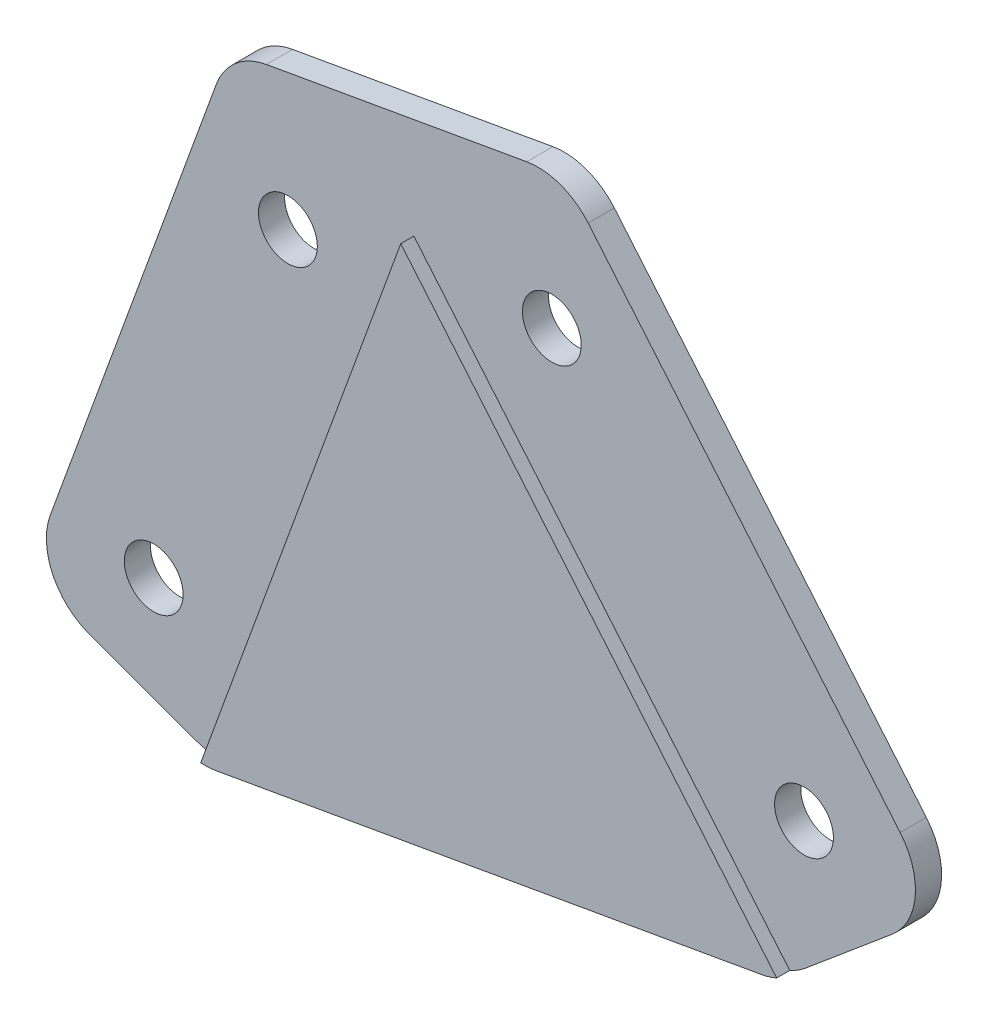
SolidWorks part; units mm, degrees
material "3.1325 (EN-AW 2017A)"
ref_plane "正面" through (0, 0, 0) normal (0, 0, 1) x (1, 0, 0)
ref_plane "平面" through (0, 0, 0) normal (0, 1, 0) x (1, 0, 0)
ref_plane "右側面" through (0, 0, 0) normal (1, 0, 0) x (0, 0, -1)
sketch "ｽｹｯﾁ1" plane through (0, 0, 0) normal (0, 0, 1) x (1, 0, 0)
  line L0 (0, 0) -> (133.1152, 365.731) construction
  line L1 (133.1152, 365.731) -> (440, 0) construction
  line L2 (440, 0) -> (0, 0) construction
  line L3 (133.1152, 365.731) -> (133.1152, 0) construction
  line L13 (133.1152, 365.731) -> (119.0198, 370.8613)
  line L14 (119.0198, 370.8613) -> (103.6289, 328.5752)
  line L15 (103.6289, 328.5752) -> (117.7243, 323.4449)
  line L16 (117.7243, 323.4449) -> (162.0407, 331.259)
  line L17 (162.0407, 331.259) -> (173.5313, 340.9009)
  line L18 (173.5313, 340.9009) -> (144.6059, 375.3729)
  line L19 (144.6059, 375.3729) -> (133.1152, 365.731)
  line L20 (144.6059, 375.3729) -> (119.0198, 370.8613)
  dimension "D4" = 15
  dimension "D5" = 15
  dimension "D6" = 45
  dimension "D1" = 440
  dimension "D2" = 70
  dimension "D3" = 50
  dimension "D7" = 45
extrude "ﾎﾞｽ - 押し出し1" add sketch "ｽｹｯﾁ1" along normal blind 3 contours L18 L19 L13 L14 L15 L16 L17 | L19 L20 L13
sketch "ｽｹｯﾁ2" plane through (0, 0, 3) normal (0, 0, 1) x (1, 0, 0)
  line L0 (103.6289, 328.5752) -> (117.7243, 323.4449) construction
  line L1 (119.0198, 370.8613) -> (103.6289, 328.5752) construction
  line L2 (173.5313, 340.9009) -> (144.6059, 375.3729) construction
  line L3 (162.0407, 331.259) -> (173.5313, 340.9009) construction
  circle A0 centre (113.2418, 333.0577) radius 2.25
  circle A1 centre (123.5024, 361.2485) radius 2.25
  circle A2 centre (143.6815, 364.8066) radius 2.25
  circle A3 centre (162.9651, 341.8253) radius 2.25
  dimension "D2" = 4.5
  dimension "D3" = 7.5
  dimension "D4" = 4.5
  dimension "D5" = 7.5
  dimension "D6" = 7.5
  dimension "D7" = 4.5
  dimension "D9" = 7.5
  dimension "D10" = 4.5
  dimension "D11" = 30
  dimension "D12" = 30
  dimension "D1" = 7.5
  dimension "D8" = 7.5
extrude "ｶｯﾄ - 押し出し1" cut sketch "ｽｹｯﾁ2" against normal blind 3
fillet "ﾌｨﾚｯﾄ1" radius 5 6 edges at (144.6059, 375.3729, 1.5) (119.0198, 370.8613, 1.5) (173.5313, 340.9009, 1.5) (162.0407, 331.259, 1.5) (117.7243, 323.4449, 1.5) (103.6289, 328.5752, 1.5)
sketch "ｽｹｯﾁ3" plane through (0, 0, 3) normal (0, 0, 1) x (1, 0, 0)
  line L0 (121.414, 377.4392) -> (103.6289, 328.5752)
  line L1 (121.414, 377.4392) -> (131.7116, 373.6912)
  line L2 (103.6289, 328.5752) -> (117.7713, 323.4278)
  line L3 (133.1326, 365.6326) -> (117.7713, 323.4278)
  line L4 (118.0325, 368.1487) -> (105.339, 333.2736) construction
  line L5 (140.1064, 380.7352) -> (173.5313, 340.9009)
  line L6 (140.1064, 380.7352) -> (131.7116, 373.6912)
  line L7 (173.5313, 340.9009) -> (162.0024, 331.2269)
  line L8 (133.1326, 365.6326) -> (162.0024, 331.2269)
  line L9 (170.3174, 344.7311) -> (146.4614, 373.1615) construction
  line L10 (108.3274, 326.8651) -> (116.4654, 323.9031) construction
  line L11 (163.067, 332.1202) -> (169.7011, 337.6869) construction
  line L13 (131.7116, 373.6912) -> (135.5563, 372.2918) construction
  line L14 (135.5563, 372.2918) -> (133.1326, 365.6326) construction
  line L15 (128.5774, 371.0612) -> (133.1326, 365.6326) construction
  line L16 (131.7116, 373.6912) -> (128.5774, 371.0612) construction
  point P18 (134.3773, 369.0525)
  dimension "D1" = 15.05
  dimension "D2" = 15.05
  dimension "D3" = 52
  dimension "D4" = 52
extrude "ｶｯﾄ - 押し出し2" cut sketch "ｽｹｯﾁ3" against normal blind 1
